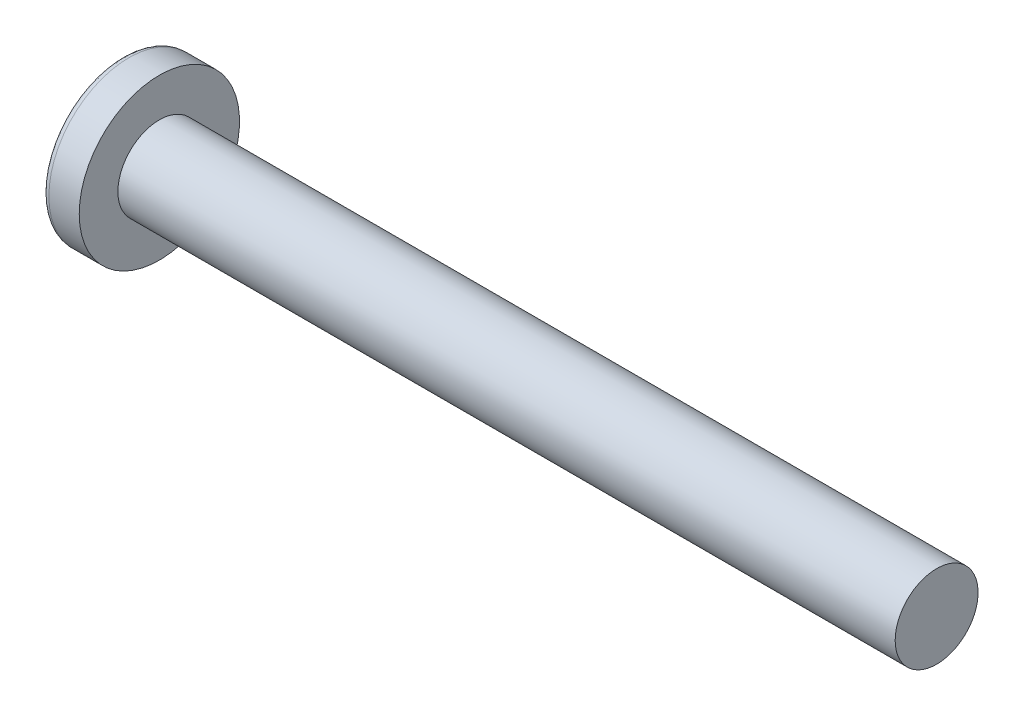
SolidWorks part; units mm, degrees
ref_plane "Plane1" through (0, 0, 0) normal (0, 0, 1) x (1, 0, 0)
ref_plane "Plane2" through (0, 0, 0) normal (0, 1, 0) x (1, 0, 0)
ref_plane "Plane3" through (0, 0, 0) normal (1, 0, 0) x (0, 0, -1)
sketch "BodySke" plane through (0, 0, 0) normal (0, 0, 1) x (1, 0, 0)
  line L0 (1.1176, 0.762) -> (1.1176, 1.4732)
  line L1 (1.2763, 6.35) -> (1.2763, -3.175) construction
  line L2 (-25.4, 0) -> (127, 0) construction
  line L3 (15.4051, 0) -> (0, 0)
  line L4 (1.1176, 0.762) -> (15.4051, 0.762)
  line L5 (15.4051, 0.762) -> (15.4051, 0)
  line L6 (0.5595, 1.4732) -> (1.1176, 1.4732)
  line L7 (1.1176, -0.762) -> (15.4051, -0.762) construction
  line L8 (1.1176, 6.35) -> (1.1176, -3.175) construction
  arc A0 (0.4562, 1.4202) -> (0, 0) centre (2.4384, 0) ccw
  arc A2 (0.4562, 1.4202) -> (0.5595, 1.4732) centre (0.5595, 1.3462) cw
  dimension "Head_crown_rad" = 2.4384
  dimension "Head_fillet_rad" = 0.127
  dimension "Diameter" = 1.524
  dimension "Head_ht" = 1.1176
  dimension "Head_dia" = 2.9464
  dimension "Advance" = 0.3175
revolve "Base-Revolve" add sketch "BodySke" angle 360 about L2
cosmetic thread "ThreadCosmetic" [suppressed] parameters "Thread_length"=2.8575, "Thread_minor"=1.1455
sketch "Sketch3" plane through (0, 0, 0) normal (1, 0, 0) x (0, 0, -1)
  line L0 (0.2794, -0.9652) -> (-0.2794, -0.9652)
  line L1 (0.2794, -0.9652) -> (0.2794, 0.9652)
  line L2 (-0.2794, 0.9652) -> (0.2794, 0.9652)
  line L3 (-0.2794, 0.9652) -> (-0.2794, -0.9652)
  dimension "Cross_dia" = 1.9304
  dimension "D1" = 0.9652
  dimension "Cross_width" = 0.5588
  dimension "D2" = 0.2794
ref_plane "Plane4" through (0.9652, 0, 0) normal (1, 0, 0) x (0, 0, -1)
sketch "Sketch4" plane through (0.9652, 0, 0) normal (1, 0, 0) x (0, 0, -1)
  line L0 (0.1397, -0.1397) -> (-0.1397, -0.1397)
  line L1 (0.1397, -0.1397) -> (0.1397, 0.1397)
  line L2 (-0.1397, 0.1397) -> (0.1397, 0.1397)
  line L3 (-0.1397, 0.1397) -> (-0.1397, -0.1397)
  dimension "D2" = 0.2794
  dimension "D1" = 0.2794
  dimension "D3" = 0.1397
  dimension "D4" = 0.1397
loft "Cut-Loft1" cut profiles "Sketch3", "Sketch4"
pattern_circular "CirPattern1" count 2 every 90 about axis through (0, 0, 0) along (1, 0, 0) of "Cut-Loft1"
sketch "ThdSchSke" plane through (0, 0, 0) normal (0, 0, 1) x (1, 0, 0)
  line L0 (1.4351, -0.5728) -> (1.3026, -0.762)
  line L1 (1.4351, -0.5728) -> (1.5676, -0.762)
  line L2 (1.5676, -0.762) -> (1.5676, -0.9525)
  line L3 (-3.175, 0) -> (5.1513, 0) construction
  line L5 (1.5676, -0.9525) -> (1.3026, -0.9525)
  line L6 (1.3026, -0.9525) -> (1.3026, -0.762)
  dimension "Diameter" = 1.524
  dimension "SideAngle" = 55
  dimension "VeeAngle" = 70
  dimension "Thread_minor" = 1.1455
  dimension "Overcut" = 1.905
  dimension "Start" = 1.4351
revolve "ThreadSchematic" [suppressed] cut sketch "ThdSchSke" angle 360 about L3
pattern_linear "ThdSchPat" [suppressed]
equation "\"D1@Sketch3\" = \"Cross_dia@Sketch3\" / 2"
equation "\"D2@Sketch3\" = \"Cross_width@Sketch3\" / 2"
equation "\"D1@Sketch4\" = \"Cross_width@Sketch3\" *.5"
equation "\"D2@Sketch4\" = \"D1@Sketch4\""
equation "\"D3@Sketch4\" = \"D1@Sketch4\" / 2"
equation "\"D4@Sketch4\" = \"D2@Sketch4\" / 2"
equation "\"Thread_length@ThreadCosmetic\" = ((sgn( (\"Length@BodySke\" - \"Advance@BodySke\" ) - \"Thread_nom@BodySke\" )-1)*( (\"Length@BodySke\" - \"Advance@BodySke\" ) - \"Thread_nom@BodySke\" ))/-2+ \"Thread_nom@BodySke\""
equation "\"Thread_minor@ThdSchSke\" = \"Thread_minor@ThreadCosmetic\""
equation "\"Diameter@ThdSchSke\" = \"Diameter@BodySke\""
equation "\"Overcut@ThdSchSke\" = \"Diameter@BodySke\" * 1.25"
equation "\"Start@ThdSchSke\" = \"Head_ht@BodySke\" + \"Length@BodySke\" - \"Thread_length@ThreadCosmetic\"  '---Non-countersunk---"
equation "\"Num_threads@ThdSchPat\" = int( \"Thread_length@ThreadCosmetic\" / \"Advance@BodySke\" + 0.999 )  + 1"
equation "\"Advance@ThdSchPat\" = \"Thread_length@ThreadCosmetic\" /  (\"Num_threads@ThdSchPat\" - 1) 'relax it"
